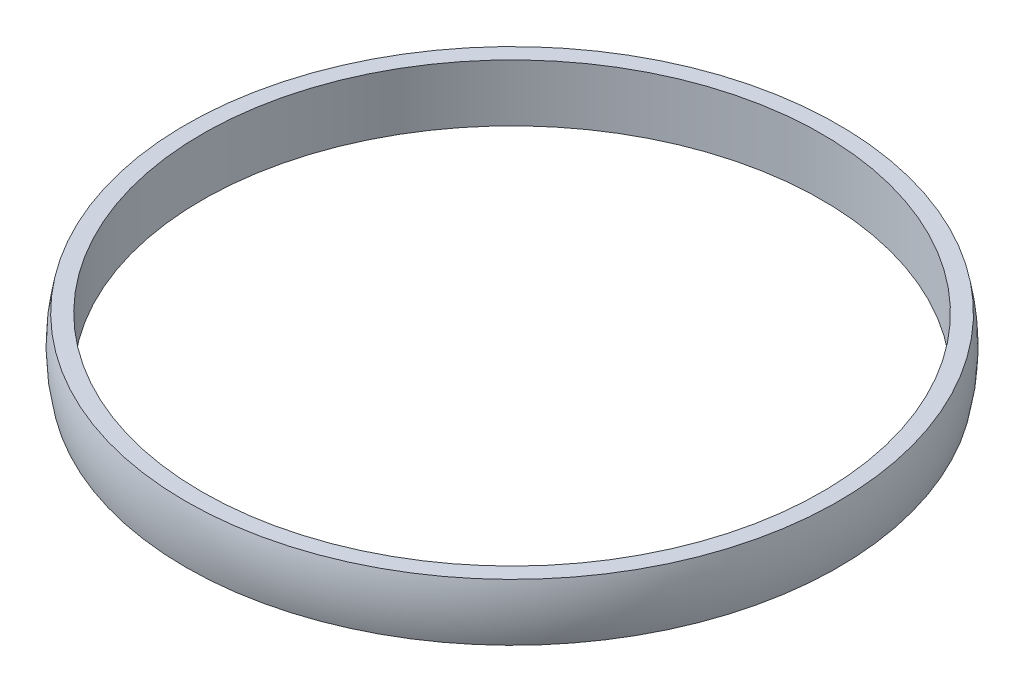
SolidWorks part; units mm, degrees
material "BUTYL"
ref_plane "Front Plane" through (0, 0, 0) normal (0, 0, 1) x (1, 0, 0)
ref_plane "Top Plane" through (0, 0, 0) normal (0, 1, 0) x (1, 0, 0)
ref_plane "Right Plane" through (0, 0, 0) normal (1, 0, 0) x (0, 0, -1)
sketch "Sketch1" plane through (0, 0, 0) normal (0, 0, 1) x (1, 0, 0)
  line L0 (0, 2.6813) -> (0, -3.0685) construction
  line L1 (38, 3.5) -> (40, 3.5)
  line L2 (38, 3.5) -> (38, -3.5)
  line L3 (38, -3.5) -> (40, -3.5)
  arc A0 (40, 3.5) -> (40, -3.5) centre (25, 0) cw
  dimension "D5" = 25
  dimension "D1" = 38
  dimension "D2" = 2
  dimension "D3" = 7
  dimension "D4" = 3.5
revolve "Revolve1" add sketch "Sketch1" angle 360 about L0
